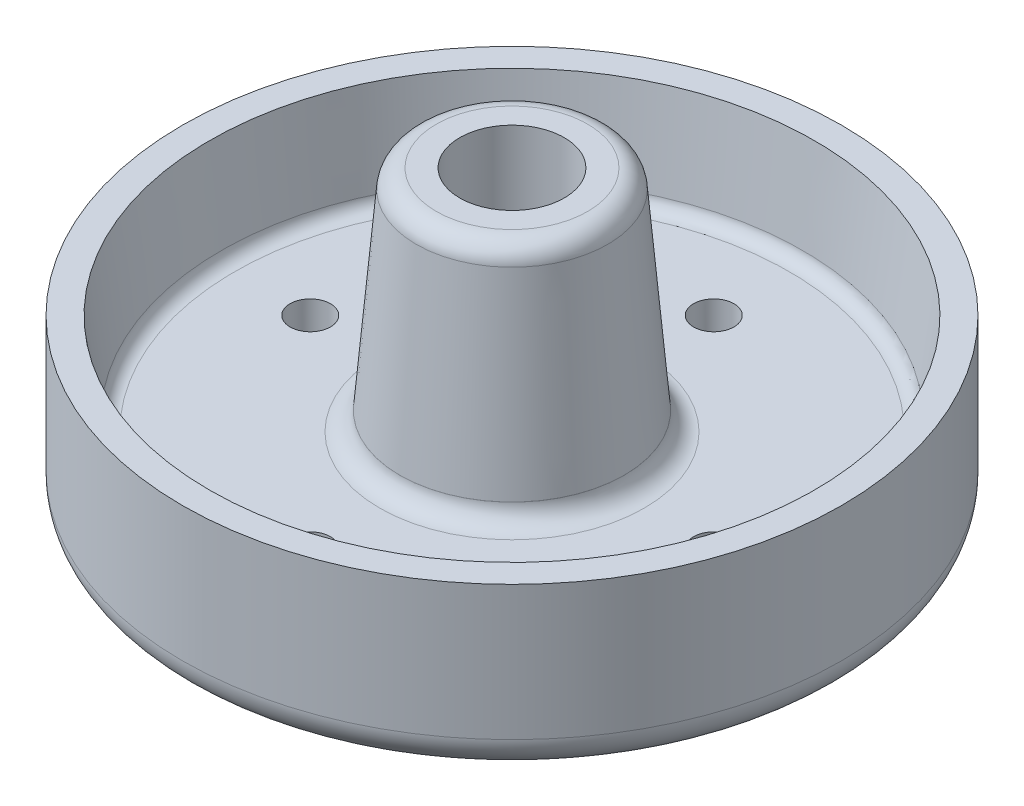
SolidWorks part; units mm, degrees
ref_plane "Front Plane" through (0, 0, 0) normal (0, 0, 1) x (1, 0, 0)
ref_plane "Top Plane" through (0, 0, 0) normal (0, 1, 0) x (1, 0, 0)
ref_plane "Right Plane" through (0, 0, 0) normal (1, 0, 0) x (0, 0, -1)
sketch "Sketch3" plane through (0, 0, 0) normal (0, 0, 1) x (1, 0, 0)
  line L0 (0, 0) -> (0, -44) construction
  line L1 (-11.2531, 0) -> (-7.7772, 0)
  line L3 (-19.6687, -34) -> (-41.249, -34) construction
  line L4 (-45, -19) -> (-43.2314, -32.2643) construction
  line L5 (-19.6687, -34) -> (-41.249, -34) construction
  line L6 (-7.7772, 0) -> (-7.7772, -47)
  line L7 (-45, -19) -> (-49, -19)
  line L8 (-49, -19) -> (-49, -39)
  line L9 (-44, -44) -> (-17, -44)
  line L12 (-7.7772, -55.4694) -> (-7.7772, 0) construction
  line L14 (-14.2421, -2.7445) -> (-16.6797, -31.2567)
  line L16 (-16.6797, -31.2567) -> (-16.6809, -31.2705) construction
  line L18 (-7.7772, -47) -> (-17, -47)
  line L19 (-17, -47) -> (-17, -44)
  line L20 (-45, -19) -> (-43.2314, -32.2643)
  line L21 (-41.249, -34) -> (-19.6687, -34)
  line L22 (-16.6809, -31.2705) -> (-16.6797, -31.2567)
  arc A0 (-14.2421, -2.7445) -> (-11.2531, 0) centre (-11.2531, -3) cw
  arc A1 (-19.6687, -34) -> (-16.6809, -31.2705) centre (-19.6687, -31) ccw
  arc A2 (-41.249, -34) -> (-43.2314, -32.2643) centre (-41.249, -32) cw
  arc A3 (-44, -44) -> (-49, -39) centre (-44, -39) cw
  point P3 (0, -22)
  point P24 (-49, -44)
  dimension "D4" = 3
  dimension "D3" = 2
  dimension "D5" = 5
  dimension "D1" = 44
  dimension "D6" = 49
  dimension "D7" = 45
  dimension "D8" = 25
revolve "Revolve3" add sketch "Sketch3" angle 360 about L0
sketch "Sketch6" plane through (0, -44, 0) normal (0, -1, 0) x (1, 0, 0)
  circle A0 centre (0, 0) radius 30
  circle A1 centre (0, 30) radius 3
  dimension "D1" = 60
  dimension "D2" = 6
extrude "Cut-Extrude2" cut sketch "Sketch6" against normal through all and the other way through all contours A1
pattern_circular "CirPattern2" count 4 over 360 about axis through (0, 0, 0) along (0, 1, 0) of "Cut-Extrude2"
